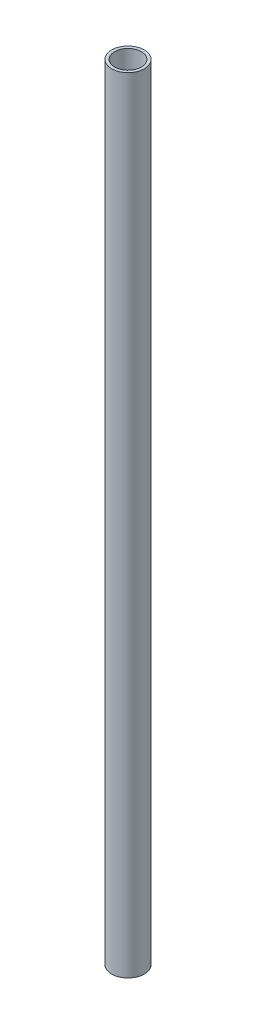
SolidWorks part; units mm, degrees
ref_plane "Front Plane" through (0, 0, 0) normal (0, 0, 1) x (1, 0, 0)
ref_plane "Top Plane" through (0, 0, 0) normal (0, 1, 0) x (1, 0, 0)
ref_plane "Right Plane" through (0, 0, 0) normal (1, 0, 0) x (0, 0, -1)
sketch "Sketch1" plane through (0, 0, 0) normal (0, 1, 0) x (1, 0, 0)
  circle A0 centre (0, 0) radius 12.7
  circle A1 centre (0, 0) radius 10.414
  dimension "D1" = 25.4
  dimension "D2" = 20.828
extrude "Boss-Extrude1" add sketch "Sketch1" along normal blind 609.6
